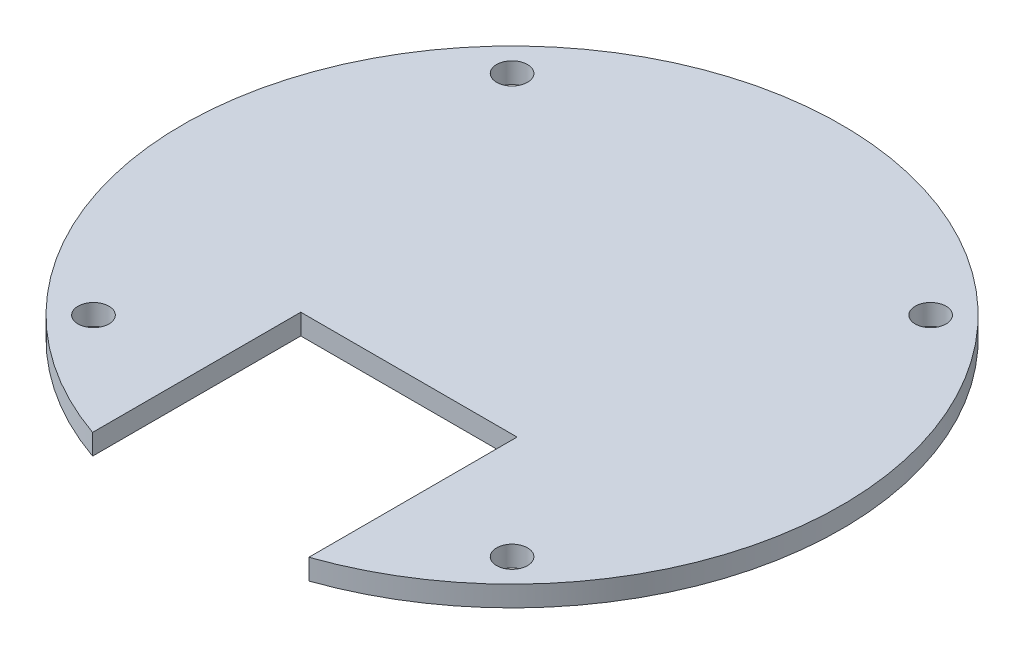
SolidWorks part; units mm, degrees
material "Epoxy, sin carga"
ref_plane "Alzado" through (0, 0, 0) normal (0, 0, 1) x (1, 0, 0)
ref_plane "Planta" through (0, 0, 0) normal (0, 1, 0) x (1, 0, 0)
ref_plane "Vista lateral" through (0, 0, 0) normal (1, 0, 0) x (0, 0, -1)
sketch "Croquis1" plane through (0, 0, 0) normal (0, 1, 0) x (1, 0, 0)
  line L0 (10.2965, -10.2341) -> (10.2965, -30.4476)
  line L1 (-10.7035, -30.4476) -> (-10.7035, -10.2341)
  line L2 (-10.7035, -10.2341) -> (10.2965, -10.2341)
  line L3 (-21.3686, 16.9506) -> (-18.2177, 17.7949)
  line L4 (-0.2035, -0.2193) -> (0, 0) construction
  line L5 (16.9665, 20.9458) -> (19.2731, 23.2524)
  line L6 (19.2731, 23.2524) -> (22.4239, 22.4081)
  line L7 (23.2682, 19.2572) -> (20.9616, 16.9506)
  line L8 (22.4239, 22.4081) -> (23.2682, 19.2572)
  line L9 (17.8107, 17.7949) -> (16.9665, 20.9458)
  line L10 (20.9616, 16.9506) -> (17.8107, 17.7949)
  line L11 (-18.2177, 17.7949) -> (-17.3734, 20.9458)
  line L12 (-22.8309, 22.4081) -> (-23.6752, 19.2572)
  line L13 (-23.6752, 19.2572) -> (-21.3686, 16.9506)
  line L14 (-19.68, 23.2524) -> (-22.8309, 22.4081)
  line L15 (-17.3734, 20.9458) -> (-19.68, 23.2524)
  line L16 (-17.3734, -21.3844) -> (-19.68, -23.691)
  line L17 (-19.68, -23.691) -> (-22.8309, -22.8467)
  line L18 (-23.6752, -19.6959) -> (-21.3686, -17.3893)
  line L19 (-22.8309, -22.8467) -> (-23.6752, -19.6959)
  line L20 (-18.2177, -18.2335) -> (-17.3734, -21.3844)
  line L21 (20.9616, -17.3893) -> (17.8107, -18.2335)
  line L22 (17.8107, -18.2335) -> (16.9665, -21.3844)
  line L23 (22.4239, -22.8467) -> (23.2682, -19.6959)
  line L24 (23.2682, -19.6959) -> (20.9616, -17.3893)
  line L25 (19.2731, -23.691) -> (22.4239, -22.8467)
  line L26 (16.9665, -21.3844) -> (19.2731, -23.691)
  line L27 (-21.3686, -17.3893) -> (-18.2177, -18.2335)
  arc A0 (10.2965, -30.4476) -> (-10.7035, -30.4476) centre (-0.2035, -0.2193) ccw
  circle A1 centre (-20.5243, 20.1015) radius 1.5
  circle A2 centre (20.1173, 20.1015) radius 1.5
  circle A3 centre (20.1173, -20.5401) radius 1.5
  circle A4 centre (-20.5243, -20.5401) radius 1.5
extrude "Saliente-Extruir2" add sketch "Croquis1" along normal blind 2 contours A0 L1 L2 L0 | A2 | A1 | A4 | A3
